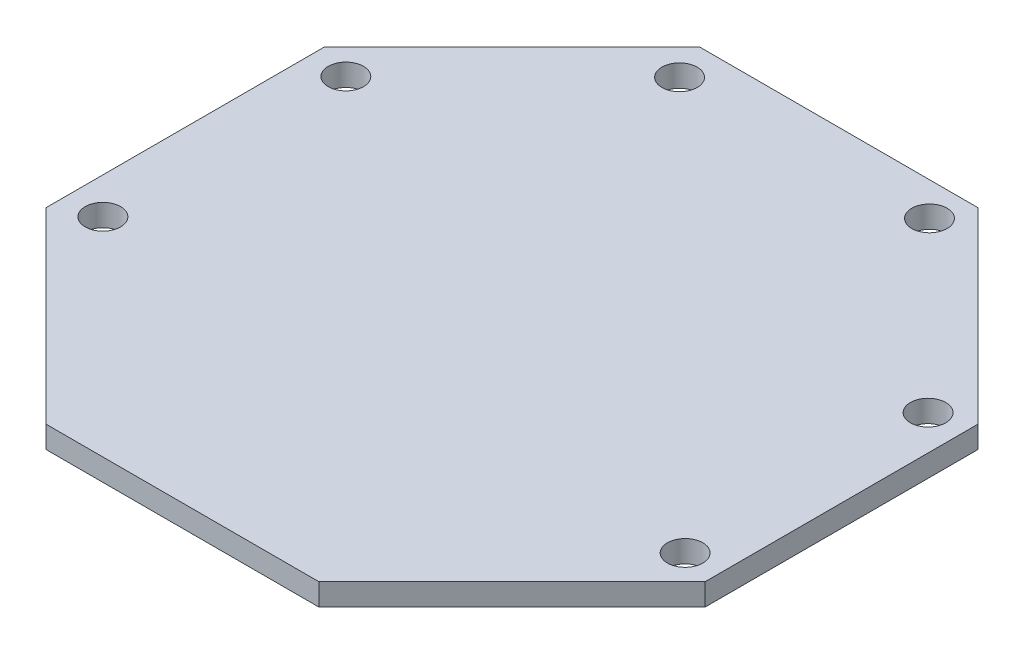
SolidWorks part; units mm, degrees
ref_plane "Front Plane" through (0, 0, 0) normal (0, 0, 1) x (1, 0, 0)
ref_plane "Top Plane" through (0, 0, 0) normal (0, 1, 0) x (1, 0, 0)
ref_plane "Right Plane" through (0, 0, 0) normal (1, 0, 0) x (0, 0, -1)
sketch "Sketch1" plane through (0, 0, 0) normal (0, 1, 0) x (1, 0, 0)
  line L0 (41.8788, 0) -> (17.0492, 0)
  line L1 (17.0492, 0) -> (0, 17.0492)
  line L2 (0, 17.0492) -> (0, 42.3868)
  line L3 (0, 42.3868) -> (17.0492, 59.436)
  line L4 (17.0492, 59.436) -> (42.3868, 59.436)
  line L5 (42.3868, 59.436) -> (59.436, 42.3868)
  line L6 (59.436, 42.3868) -> (59.436, 17.5572)
  line L7 (59.436, 17.5572) -> (41.8788, 0)
  circle A0 centre (56.261, 18.923) radius 1.6055
  circle A1 centre (56.261, 41.021) radius 1.6055
  circle A2 centre (41.021, 56.388) radius 1.6055
  circle A3 centre (18.542, 56.134) radius 1.6055
  circle A4 centre (3.302, 41.021) radius 1.6055
  circle A5 centre (3.302, 18.923) radius 1.6055
  point P21 (40.216, 31.4989)
  point P22 (42.1963, 1.7761)
  dimension "D1" = 3.211
  dimension "D2" = 3.211
  dimension "D3" = 3.211
  dimension "D4" = 3.211
  dimension "D5" = 3.211
  dimension "D6" = 3.211
  dimension "D7" = 3.302
  dimension "D8" = 3.302
  dimension "D9" = 17.0492
  dimension "D10" = 17.0492
  dimension "D11" = 18.542
  dimension "D12" = 41.021
  dimension "D13" = 41.8788
  dimension "D14" = 42.3868
  dimension "D15" = 59.436
  dimension "D16" = 17.0492
  dimension "D17" = 17.5572
  dimension "D18" = 56.134
  dimension "D19" = 56.261
  dimension "D20" = 56.261
  dimension "D21" = 56.388
  dimension "D22" = 18.923
  dimension "D23" = 18.923
  dimension "D24" = 41.021
  dimension "D25" = 41.021
  dimension "D26" = 42.3868
  dimension "D27" = 42.3868
  dimension "D28" = 59.436
extrude "Boss-Extrude1" add sketch "Sketch1" along normal blind 2
